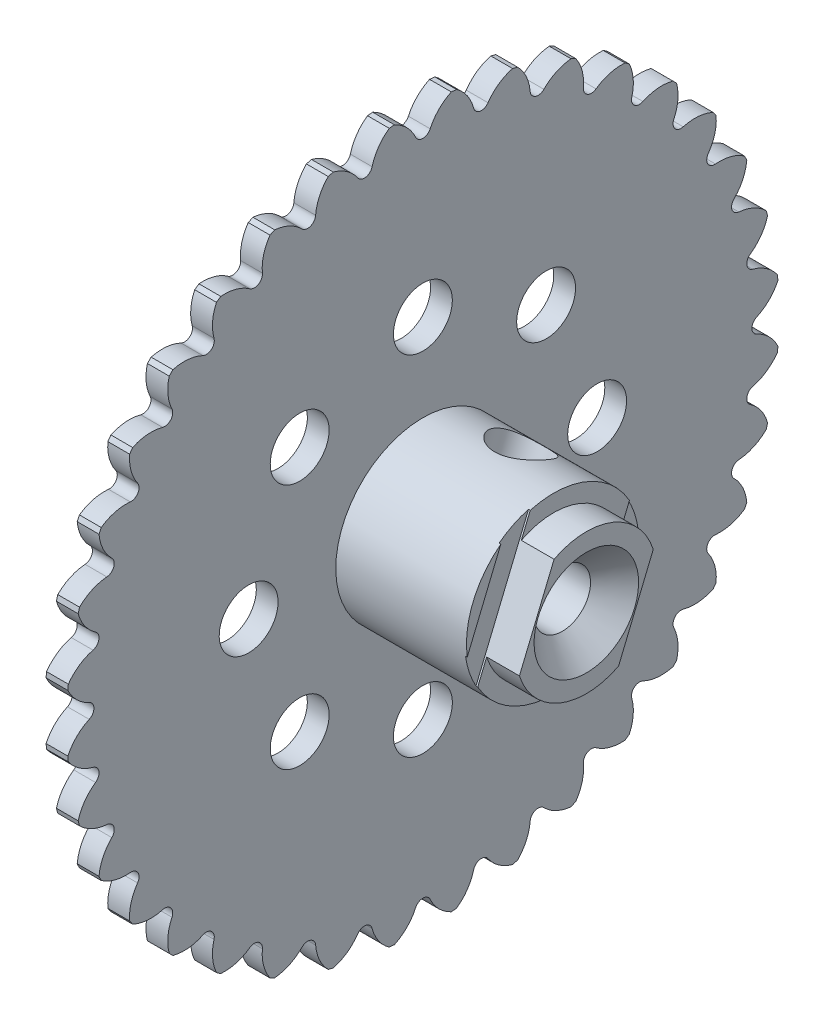
SolidWorks part; units mm, degrees
material "Brass"
ref_plane "Front Plane" through (0, 0, 0) normal (0, 0, 1) x (1, 0, 0)
ref_plane "Top Plane" through (0, 0, 0) normal (0, 1, 0) x (1, 0, 0)
ref_plane "Right Plane" through (0, 0, 0) normal (1, 0, 0) x (0, 0, -1)
sketch "Sketch1" plane through (0, 0, 0) normal (1, 0, 0) x (0, 0, -1)
  circle A0 centre (0, 0) radius 25.9588
  dimension "D1" = 51.9176
extrude "Boss-Extrude1" add sketch "Sketch1" along normal blind 1.5875
sketch "Sketch2" plane through (1.5875, 0, 0) normal (1, 0, 0) x (0, 0, -1)
  circle A0 centre (0, 0) radius 12.7 construction
  circle A1 centre (0, 12.7) radius 2.1463
  dimension "D1" = 25.4
  dimension "D2" = 4.2926
extrude "Cut-Extrude1" cut sketch "Sketch2" against normal blind 1.5875
pattern_circular "CirPattern1" count 8 over 360 about axis through (0, 0, 0) along (1, 0, 0) of "Cut-Extrude1"
sketch "Sketch4" plane through (1.5875, 0, 0) normal (1, 0, 0) x (0, 0, -1)
  line L0 (0, 23.9776) -> (0, 25.9588) construction
  line L1 (0, 0.8731) -> (0, -0.8731) construction
  line L2 (0, 0) -> (-2.0726, 25.8759) construction
  line L3 (0, 0) -> (2.4522, 25.8427) construction
  arc A0 (-2.0726, 25.8759) -> (-0.5315, 24.3192) centre (-3.4198, 23.0009) cw
  circle A1 centre (0, 0) radius 25.9588 construction
  arc A2 (-0.5315, 24.3192) -> (0.5315, 24.3192) centre (0, 24.5618) ccw
  arc A3 (0.5315, 24.3192) -> (2.0726, 25.8759) centre (3.4198, 23.0009) cw
  arc A4 (-2.0726, 25.8759) -> (2.4522, 25.8427) centre (0, 0) cw
  circle M13 centre (0, 0) radius 25.9588
  dimension "D1" = 0.5842
  dimension "D2" = 3.175
  dimension "D3" = 1.9812
  dimension "D4" = 10
  dimension "D5" = 0.381
extrude "Cut-Extrude2" cut sketch "Sketch4" against normal blind 1.5875 contours A2 A3 A0 M13
pattern_circular "CirPattern2" count 36 over 360 about axis through (0, 0, 0) along (1, 0, 0) of "Cut-Extrude2"
sketch "Sketch7" plane through (1.5875, 0, 0) normal (1, 0, 0) x (0, 0, -1)
  circle A0 centre (0, 0) radius 6.35
  dimension "D1" = 12.7
extrude "Boss-Extrude3" add sketch "Sketch7" along normal blind 9.525
sketch "Sketch8" plane through (11.1125, 0, 0) normal (1, 0, 0) x (0, 0, -1)
  line L0 (-4.877, -1.5525) -> (-2.3507, 4.5463)
  line L1 (2.3507, -4.5463) -> (4.877, 1.5525)
  line L3 (0, 5.1181) -> (0, -5.1181) construction
  arc A0 (-4.877, -1.5525) -> (2.3507, -4.5463) centre (0, 0) ccw
  arc A1 (4.877, 1.5525) -> (-2.3507, 4.5463) centre (0, 0) ccw
  dimension "D3" = 10.2362
  dimension "D1" = 22.5
  dimension "D2" = 7.8232
extrude "Boss-Extrude4" add sketch "Sketch8" along normal blind 2.3876
sketch "Sketch9" plane through (13.5001, 0, 0) normal (1, 0, 0) x (0, 0, -1)
  circle A0 centre (0, 0) radius 2.0574
  dimension "D1" = 4.1148
extrude "Cut-Extrude3" cut sketch "Sketch9" against normal through all contours A0
sketch "Sketch10" plane through (11.1125, 0, 0) normal (1, 0, 0) x (0, 0, -1)
  line L0 (-5.5281, -3.1245) -> (-1.6996, 6.1183)
  line L1 (-2.3507, 4.5463) -> (-4.877, -1.5525) construction
  line L2 (-6.2923, -0.8542) -> (-3.8453, 5.0534)
  line L3 (-3.9537, -9.545) -> (3.9537, 9.545) construction
  line L4 (3.8453, -5.0534) -> (6.2923, 0.8542)
  line L5 (1.6996, -6.1183) -> (5.5281, 3.1245)
  circle A0 centre (0, 0) radius 6.35 construction
  circle A1 centre (0, 0) radius 6.35 construction
  arc A4 (-1.6996, 6.1183) -> (-3.8453, 5.0534) centre (0, 0) ccw
  arc A5 (-5.5281, -3.1245) -> (-6.2923, -0.8542) centre (0, 0) cw
  arc A6 (1.6996, -6.1183) -> (3.8453, -5.0534) centre (0, 0) ccw
  arc A7 (5.5281, 3.1245) -> (6.2923, 0.8542) centre (0, 0) cw
  point P17 (0, 0)
  dimension "D1" = 1.5748
extrude "Cut-Extrude4" cut sketch "Sketch10" against normal blind 0.127
sketch "Sketch11" plane through (0, 0, 0) normal (0, 0, 1) x (1, 0, 0)
  line L3 (13.5001, -3.81) -> (13.5001, 3.81)
  line L5 (13.5001, 4.5463) -> (13.5001, -1.5525) construction
  line L6 (13.5001, 3.81) -> (9.6901, 0)
  line L7 (9.6901, 0) -> (13.5001, -3.81)
  line L8 (13.5001, 0) -> (9.6901, 0) construction
  point P3 (13.5001, 0)
  dimension "D1" = 90
  dimension "D2" = 7.62
revolve "Cut-Revolve4" cut sketch "Sketch11" angle 360 about L8
ref_plane "Plane1" through (0, 0, 0) normal (0, -0.3827, -0.9239) x (-1, 0, 0)
sketch "Sketch12" plane through (0, 0, 0) normal (0, -0.3827, -0.9239) x (-1, 0, 0)
  line L0 (-6.35, -6.35) -> (-6.35, 6.35)
  line L1 (-1.5875, 6.35) -> (-11.1125, 6.35) construction
  line L2 (-8.3344, -6.35) -> (-8.3344, 6.35)
  line L3 (-11.1125, -6.35) -> (-1.5875, -6.35) construction
  line L4 (-8.3344, 6.35) -> (-6.35, 6.35)
  line L5 (-8.3344, -6.35) -> (-6.35, -6.35)
  point P5 (-6.35, 0)
  dimension "D1" = 4.7625
  dimension "D2" = 1.9844
revolve "Cut-Revolve5" cut sketch "Sketch12" angle 360 about L0
